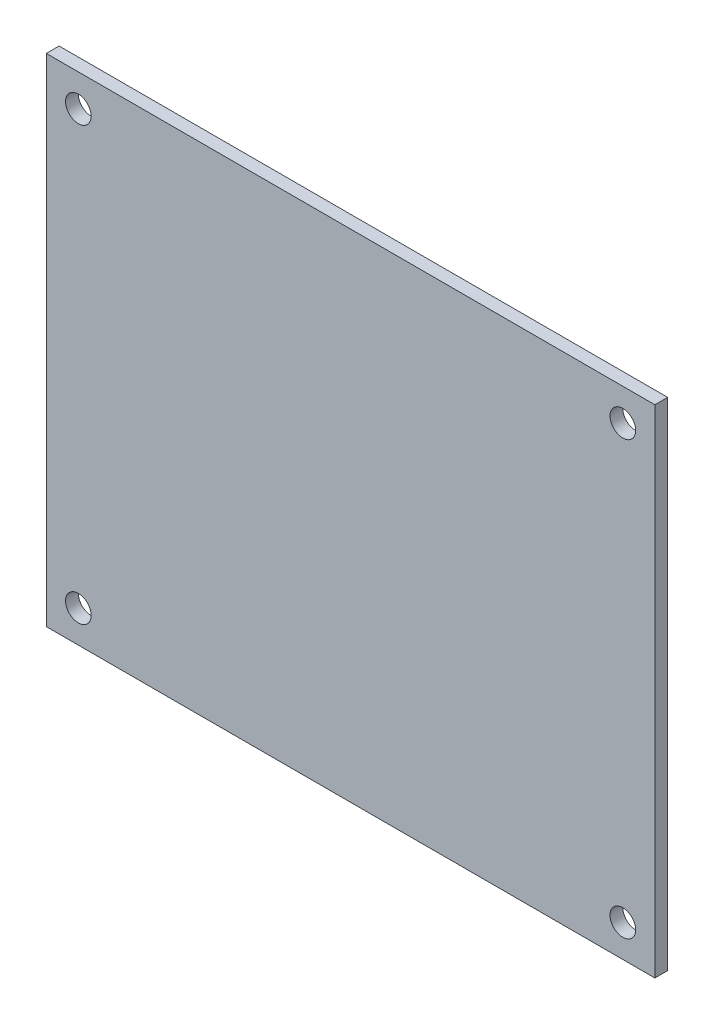
SolidWorks part; units mm, degrees
ref_plane "Front Plane" through (0, 0, 0) normal (0, 0, 1) x (1, 0, 0)
ref_plane "Top Plane" through (0, 0, 0) normal (0, 1, 0) x (1, 0, 0)
ref_plane "Right Plane" through (0, 0, 0) normal (1, 0, 0) x (0, 0, -1)
sketch "Sketch1" plane through (0, 0, 0) normal (0, 0, 1) x (1, 0, 0)
  line L1 (-38, 31) -> (38, 31)
  line L2 (-38, 31) -> (-38, -31)
  line L3 (-38, -31) -> (38, -31)
  line L4 (38, 31) -> (38, -31)
  circle A0 centre (-34, 27) radius 1.6
  circle A1 centre (34, 27) radius 1.6
  circle A2 centre (34, -27) radius 1.6
  circle A3 centre (-34, -27) radius 1.6
  point P4 (0, 31)
  point P5 (38, 0)
  point P15 (0, 0)
  point P16 (0, 0)
  point P17 (0, 0)
  point P18 (0, 0)
  dimension "D3" = 3.2
  dimension "D1" = 76
  dimension "D2" = 62
  dimension "D4" = 4
  dimension "D5" = 4
  dimension "D6" = 4
  dimension "D7" = 4
extrude "Main" add sketch "Sketch1" along normal blind 1.6
